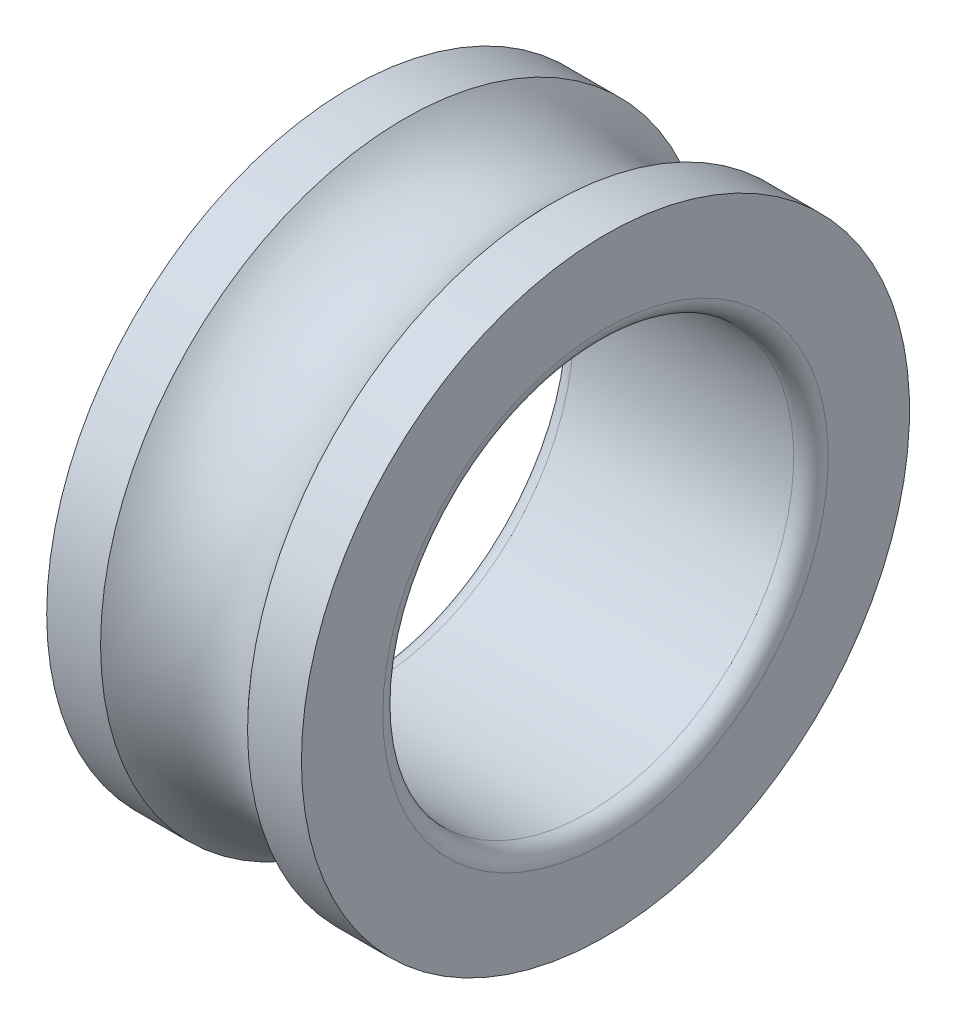
SolidWorks part; units mm, degrees
ref_plane "Front Plane" through (0, 0, 0) normal (0, 0, 1) x (1, 0, 0)
ref_plane "Top Plane" through (0, 0, 0) normal (0, 1, 0) x (1, 0, 0)
ref_plane "Right Plane" through (0, 0, 0) normal (1, 0, 0) x (0, 0, -1)
sketch "Sketch1" plane through (0, 0, 0) normal (0, 0, 1) x (1, 0, 0)
  line L0 (-29.5833, 0) -> (33.75, 0) construction
  line L1 (0, 0) -> (0, 25) construction
  line L2 (-15.5, 37) -> (-8.9443, 37)
  line L3 (-15.5, 37) -> (-15.5, 27.1)
  line L4 (-13.4, 25) -> (13.4, 25)
  line L5 (15.5, 37) -> (15.5, 27.1)
  line L6 (-15.5, 37) -> (15.5, 25) construction
  line L7 (-15.5, 25) -> (15.5, 37) construction
  line L8 (8.9443, 37) -> (15.5, 37)
  arc A0 (-8.9443, 37) -> (8.9443, 37) centre (0, 45) ccw
  arc A1 (13.4, 25) -> (15.5, 27.1) centre (13.4, 27.1) ccw
  arc A2 (-15.5, 27.1) -> (-13.4, 25) centre (-13.4, 27.1) ccw
  point P3 (0, 31)
  dimension "D5" = 12
  dimension "D6" = 2.1
  dimension "D1" = 31
  dimension "D2" = 25
  dimension "D3" = 37
  dimension "D4" = 8
revolve "Revolve1" add sketch "Sketch1" angle 360 about L0
